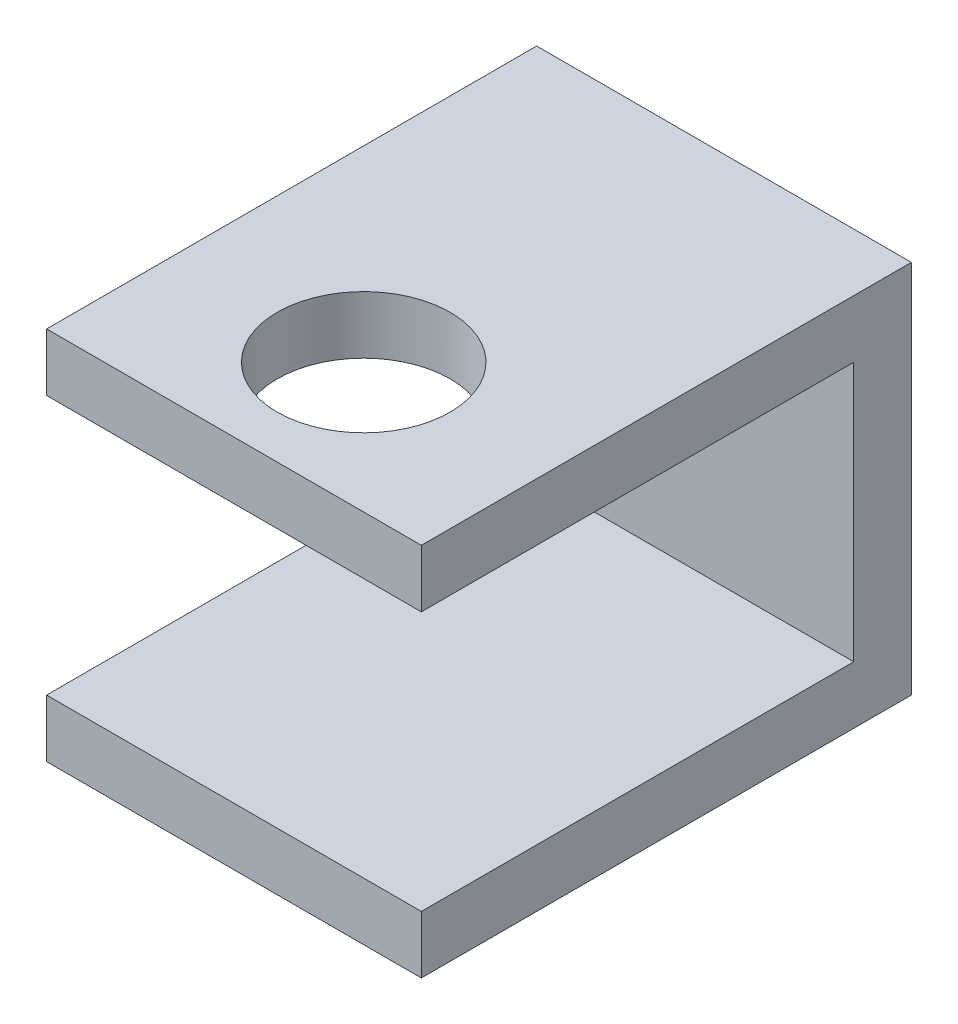
SolidWorks part; units mm, degrees
ref_plane "Front Plane" through (0, 0, 0) normal (0, 0, 1) x (1, 0, 0)
ref_plane "Top Plane" through (0, 0, 0) normal (0, 1, 0) x (1, 0, 0)
ref_plane "Right Plane" through (0, 0, 0) normal (1, 0, 0) x (0, 0, -1)
sketch "Sketch2" plane through (0, 0, 0) normal (0, 0, 1) x (1, 0, 0)
  line L1 (0, 0) -> (1.3, 0)
  line L2 (0, 0) -> (0, 1.3)
  line L3 (0, 1.3) -> (1.3, 1.3)
  line L4 (1.3, 0) -> (1.3, 1.3)
  dimension "D1" = 1.3
  dimension "D2" = 1.3
extrude "Boss-Extrude2" add sketch "Sketch2" along normal blind 1.7
sketch "Sketch10" plane through (0, 0, 1.7) normal (0, 0, 1) x (1, 0, 0)
  line L0 (0, 1.3) -> (0, 0) construction
  line L1 (0, 1.1) -> (1.3, 1.1)
  line L2 (0, 1.1) -> (0, 0.2)
  line L3 (0, 0.2) -> (1.3, 0.2)
  line L4 (1.3, 1.1) -> (1.3, 0.2)
  line L5 (1.3, 0) -> (1.3, 1.3) construction
  line L6 (1.3, 1.3) -> (0, 1.3) construction
  dimension "D1" = 0.2
  dimension "D2" = 0.9
extrude "Cut-Extrude4" cut sketch "Sketch10" against normal blind 2 contours L1 L4 L3 L2
sketch "Sketch12" plane through (0, 1.3, 0) normal (0, 1, 0) x (1, 0, 0)
  line L0 (0.65, -1.7) -> (0.65, 0) construction
  line L1 (1.3, -1.7) -> (0, -1.7) construction
  line L2 (1.3, 0) -> (0, 0) construction
  circle A0 centre (0.65, -1.25) radius 0.3
  dimension "D1" = 0.6
  dimension "D2" = 0.45
extrude "Cut-Extrude5" cut sketch "Sketch12" against normal blind 1.3
sketch "Sketch14" plane through (0, 0, 0) normal (0, 0, -1) x (-1, 0, 0)
  line L1 (-1.3, 1.3) -> (0, 1.3)
  line L2 (-1.3, 1.3) -> (-1.3, 0)
  line L3 (-1.3, 0) -> (0, 0)
  line L4 (0, 1.3) -> (0, 0)
extrude "Boss-Extrude3" add sketch "Sketch14" against normal blind 0.2
